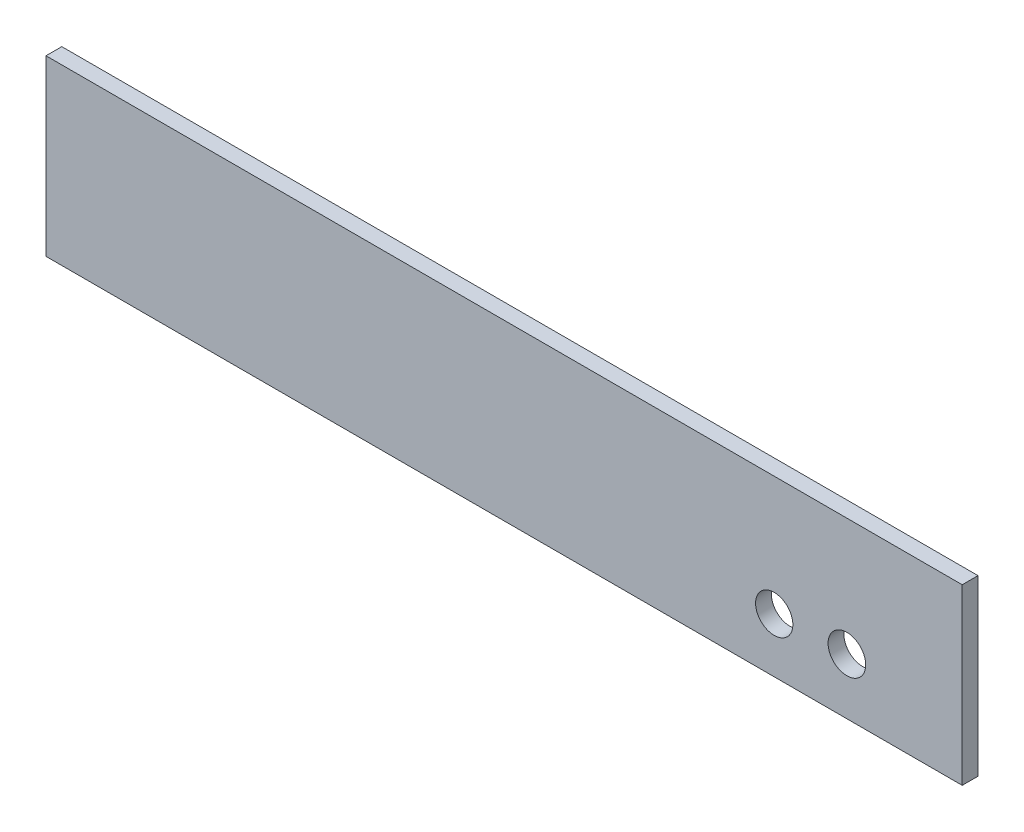
SolidWorks part; units mm, degrees
ref_plane "Plan de face" through (0, 0, 0) normal (0, 0, 1) x (1, 0, 0)
ref_plane "Plan de dessus" through (0, 0, 0) normal (0, 1, 0) x (1, 0, 0)
ref_plane "Plan de droite" through (0, 0, 0) normal (1, 0, 0) x (0, 0, -1)
sketch "Esquisse1" plane through (0, 0, 0) normal (0, 0, 1) x (1, 0, 0)
  line L1 (0, 0) -> (580, 0)
  line L2 (0, 0) -> (0, 110)
  line L3 (0, 110) -> (580, 110)
  line L4 (580, 0) -> (580, 110)
  dimension "D1" = 580
  dimension "D2" = 110
extrude "Boss.-Extru.1" add sketch "Esquisse1" along normal blind 10
sketch "Esquisse2" plane through (0, 0, 0) normal (0, 0, -1) x (-1, 0, 0)
  circle A0 centre (-461, 34.5) radius 11.8
  circle A1 centre (-507, 35.5) radius 11.9
extrude "Enlèv. mat.-Extru.1" cut sketch "Esquisse2" against normal blind 10
